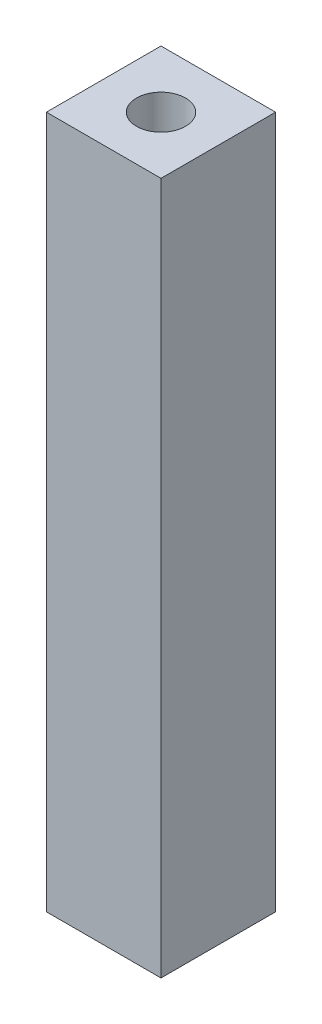
SolidWorks part; units mm, degrees
ref_plane "Alzado" through (0, 0, 0) normal (0, 0, 1) x (1, 0, 0)
ref_plane "Planta" through (0, 0, 0) normal (0, 1, 0) x (1, 0, 0)
ref_plane "Vista lateral" through (0, 0, 0) normal (1, 0, 0) x (0, 0, -1)
sketch "Croquis1" plane through (0, 0, 0) normal (0, 1, 0) x (1, 0, 0)
  line L1 (0, 0) -> (9.1, 0)
  line L2 (0, 0) -> (0, 9.1)
  line L3 (0, 9.1) -> (9.1, 9.1)
  line L4 (9.1, 0) -> (9.1, 9.1)
  dimension "D1" = 9.1
  dimension "D2" = 9.1
extrude "Saliente-Extruir1" add sketch "Croquis1" along normal blind 55
sketch "Croquis2" plane through (0, 55, 0) normal (0, 1, 0) x (1, 0, 0)
  circle A2 centre (4.55, 4.55) radius 1.95
  dimension "D1" = 3.9
extrude "Cortar-Extruir1" cut sketch "Croquis2" against normal blind 13
sketch "Croquis3" plane through (0, 0, 0) normal (0, -1, 0) x (1, 0, 0)
  circle A0 centre (4.55, -4.55) radius 1.95 construction
  circle A1 centre (4.55, -4.55) radius 1.95
extrude "Cortar-Extruir2" cut sketch "Croquis3" against normal blind 10
